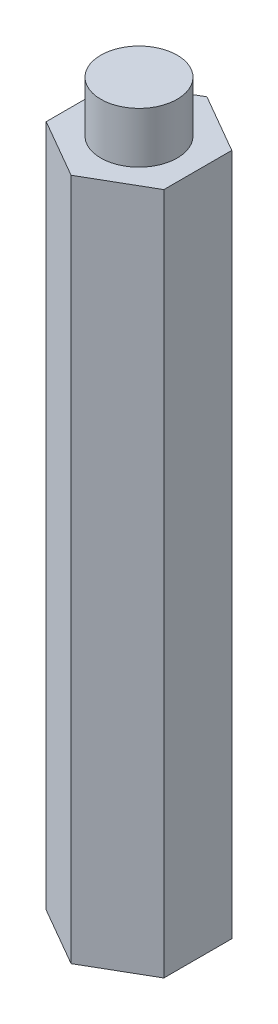
SolidWorks part; units mm, degrees
ref_plane "Front Plane" through (0, 0, 0) normal (0, 0, 1) x (1, 0, 0)
ref_plane "Top Plane" through (0, 0, 0) normal (0, 1, 0) x (1, 0, 0)
ref_plane "Right Plane" through (0, 0, 0) normal (1, 0, 0) x (0, 0, -1)
sketch "Sketch1" plane through (0, 0, 0) normal (0, 1, 0) x (1, 0, 0)
  line L1 (0, -4) -> (3.4641, -2)
  line L2 (3.4641, -2) -> (3.4641, 2)
  line L3 (3.4641, 2) -> (0, 4)
  line L4 (0, 4) -> (-3.4641, 2)
  line L5 (-3.4641, 2) -> (-3.4641, -2)
  line L6 (-3.4641, -2) -> (0, -4)
  circle A0 centre (0, 0) radius 3.4641 construction
  dimension "D1" = 4
extrude "Boss-Extrude1" add sketch "Sketch1" along normal blind 40.21
sketch "Sketch2" plane through (0, 40.21, 0) normal (0, 1, 0) x (1, 0, 0)
  circle A0 centre (0, 0) radius 2.25
extrude "Boss-Extrude2" add sketch "Sketch2" along normal blind 3 and the other way blind 30
